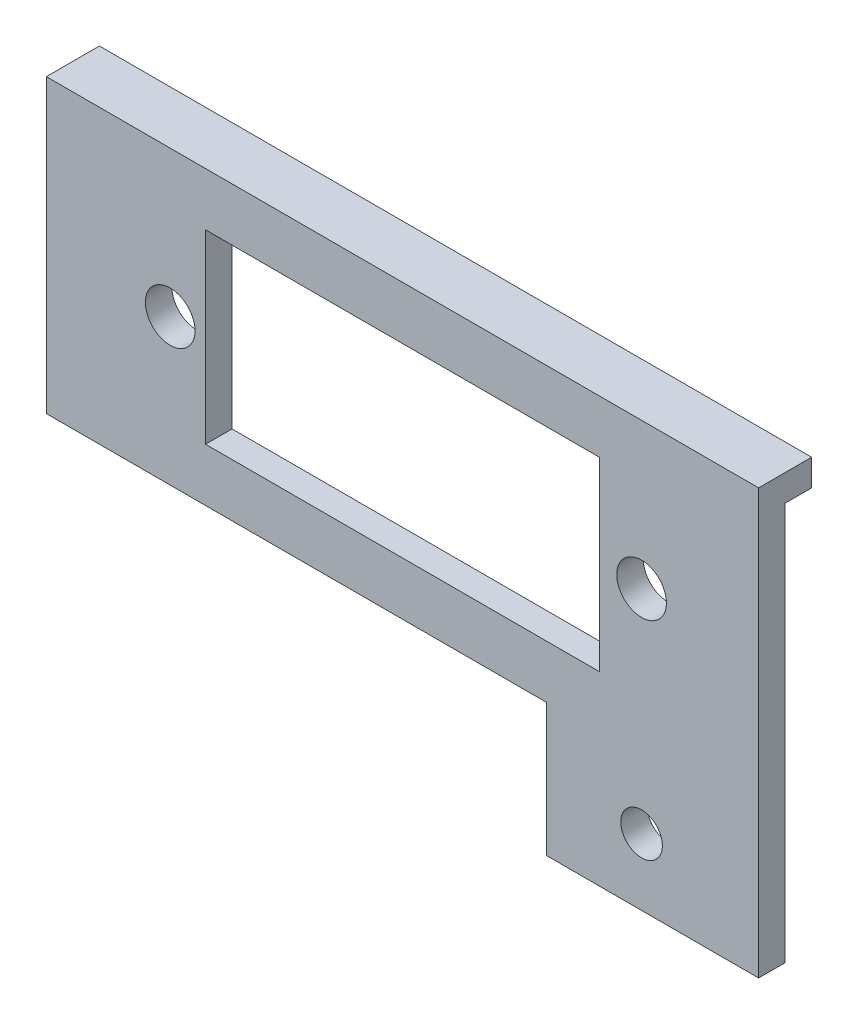
SolidWorks part; units mm, degrees
material "6061-T6 (SS)"
ref_plane "Front Plane" through (0, 0, 0) normal (0, 0, 1) x (1, 0, 0)
ref_plane "Top Plane" through (0, 0, 0) normal (0, 1, 0) x (1, 0, 0)
ref_plane "Right Plane" through (0, 0, 0) normal (1, 0, 0) x (0, 0, -1)
sketch "Sketch1" plane through (0, 0, 0) normal (0, 0, 1) x (1, 0, 0)
  line L0 (31.3778, 1.6002) -> (-39.4374, 1.6002) construction
  line L1 (18.4277, 3.1877) -> (-28.7147, 3.1877)
  line L2 (18.4277, 3.1877) -> (18.4277, -19.0373)
  line L3 (18.4277, -19.0373) -> (-28.7147, -19.0373)
  line L4 (-28.7147, 3.1877) -> (-28.7147, -19.0373)
  line L5 (31.3778, -17.4498) -> (-39.4374, -17.4498) construction
  line L6 (16.8402, -15.8496) -> (16.8402, 0.0127) construction
  line L7 (-27.1272, -17.4371) -> (-27.1272, 1.6002) construction
  line L8 (24.7777, 9.5377) -> (-35.0647, 9.5377)
  line L9 (-35.0647, 9.5377) -> (-35.0647, -25.3873) construction
  line L10 (24.7777, -25.3873) -> (-35.0647, -25.3873)
  line L11 (24.7777, 9.5377) -> (24.7777, -25.3873) construction
  line L12 (-47.7647, 22.2377) -> (-47.7647, -25.3873)
  line L13 (37.4777, 22.2377) -> (-47.7647, 22.2377) construction
  line L14 (37.4777, 22.2377) -> (37.4777, -25.3873)
  line L15 (24.7777, 9.5377) -> (37.4777, 9.5377)
  line L16 (-35.0647, 9.5377) -> (-47.7647, 9.5377)
  line L17 (37.4777, 22.2377) -> (37.4777, -19.0373) construction
  line L18 (-47.7647, 22.2377) -> (-47.7647, -19.0373) construction
  line L19 (-35.0647, -25.3873) -> (-47.7647, -25.3873)
  line L20 (37.4777, -25.3873) -> (24.7777, -25.3873)
  line L22 (37.4777, -25.3873) -> (12.0777, -25.3873)
  line L23 (37.4777, -25.3873) -> (37.4777, -41.2623)
  line L24 (37.4777, -41.2623) -> (12.0777, -41.2623)
  line L25 (12.0777, -25.3873) -> (12.0777, -41.2623)
  circle A0 centre (23.4716, -7.9248) radius 2.9718 construction
  circle A1 centre (-32.9418, -7.9248) radius 2.9718 construction
  circle A2 centre (23.4716, -7.9248) radius 2.9718
  circle A3 centre (-32.9418, -7.9248) radius 2.9718
  circle A4 centre (23.4716, -33.3248) radius 2.4892
  dimension "D9" = 25.4
  dimension "D10" = 4.9784
  dimension "D1" = 1.5875
  dimension "D2" = 1.5875
  dimension "D3" = 1.5875
  dimension "D4" = 1.5875
  dimension "D7" = 25.4
  dimension "D8" = 50.8
  dimension "D5" = 6.35
  dimension "D6" = 19.05
extrude "Boss-Extrude1" add sketch "Sketch1" along normal blind 3.175 contours L20 L14 L15 L8 L16 L12 L19 L10 A3 A2 L4 L1 L2 L3 | L10 L25 L24 L23 L20 A4
sketch "Sketch2" plane through (0, 0, 0) normal (0, 0, -1) x (-1, 0, 0)
  line L0 (47.7647, 9.5377) -> (47.7647, -25.3873) construction
  line L1 (-37.4777, 9.5377) -> (47.7647, 9.5377)
  line L2 (-37.4777, 9.5377) -> (-37.4777, 6.3627)
  line L3 (-37.4777, 6.3627) -> (47.7647, 6.3627)
  line L4 (47.7647, 9.5377) -> (47.7647, 6.3627)
  dimension "D1" = 3.175
extrude "Boss-Extrude2" add sketch "Sketch2" along normal blind 3.175
equation "\"Thick\"= \"in\""
